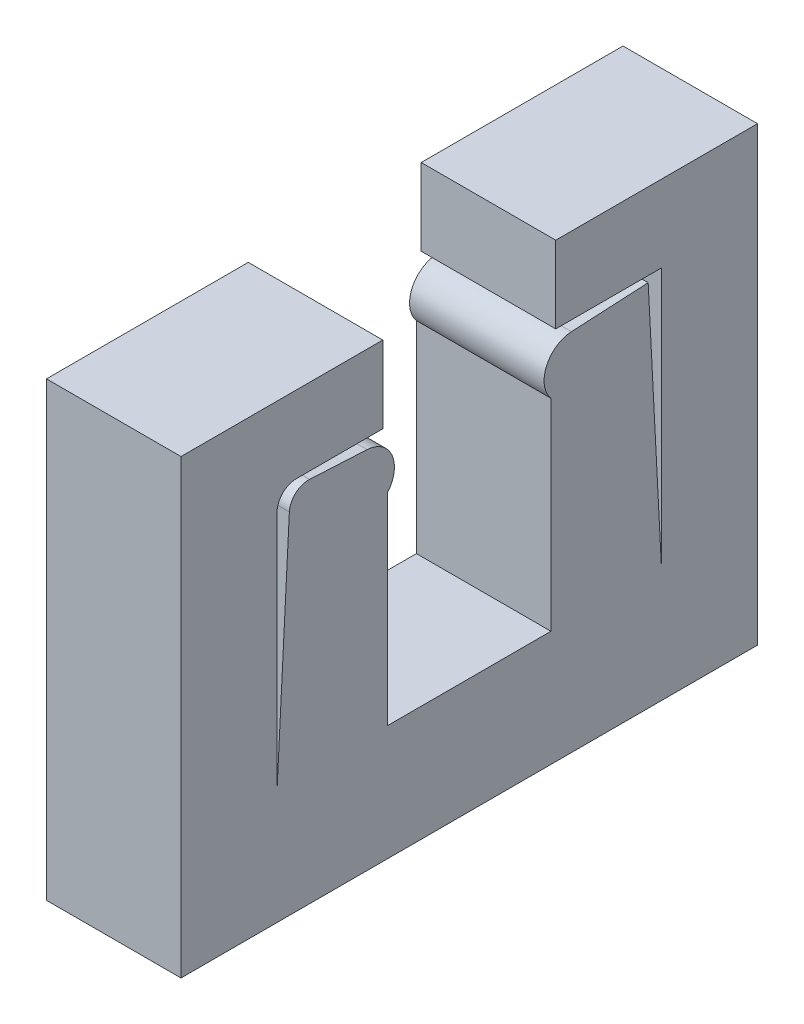
SolidWorks part; units mm, degrees
ref_plane "Front Plane" through (0, 0, 0) normal (0, 0, 1) x (1, 0, 0)
ref_plane "Top Plane" through (0, 0, 0) normal (0, 1, 0) x (1, 0, 0)
ref_plane "Right Plane" through (0, 0, 0) normal (1, 0, 0) x (0, 0, -1)
sketch "Sketch4" plane through (0, 0, 0) normal (1, 0, 0) x (0, 0, -1)
  line L0 (-82.5369, 31.7713) -> (-81.8462, 44.9496)
  line L1 (-76.7869, 42.2713) -> (-76.7869, 31.7713)
  line L2 (-87.5369, 49.2713) -> (-87.5369, 25.7713)
  line L4 (-82.5369, 45.2713) -> (-82.5369, 31.7713)
  line L5 (-76.7869, 31.7713) -> (-72.5369, 31.7713)
  line L7 (-87.5369, 25.7713) -> (-72.5369, 25.7713)
  line L8 (-72.5369, 31.7713) -> (-72.5369, 25.7713)
  line L9 (-82.5369, 45.2713) -> (-77.0369, 45.2713)
  line L11 (-87.5369, 49.2713) -> (-77.0369, 49.2713)
  line L12 (-77.0369, 45.2713) -> (-77.0369, 49.2713)
  line L14 (-81.8462, 44.9496) -> (-77.8517, 44.7402)
  arc A0 (-77.8517, 44.7402) -> (-76.7869, 42.2713) centre (-77.9302, 43.2423) cw
  dimension "D9" = 1.5
  dimension "D1" = 13.5
  dimension "D2" = 4
  dimension "D3" = 5
  dimension "D4" = 4.25
  dimension "D5" = 6
  dimension "D6" = 10
  dimension "D7" = 3
  dimension "D8" = 10.5
  dimension "D10" = 4
  dimension "D11" = 13.5
extrude "Boss-Extrude2" add sketch "Sketch4" along normal blind 7
fillet "Fillet1" radius 1 1 edges at (3.5, 44.9496, 81.8462)
fillet "Fillet2" radius 1 1 edges at (3.5, 45.2713, 82.5369)
mirror "Mirror2" about plane through (7, 31.7713, 72.5369) normal (0, 0, 1) of "Boss-Extrude2"
